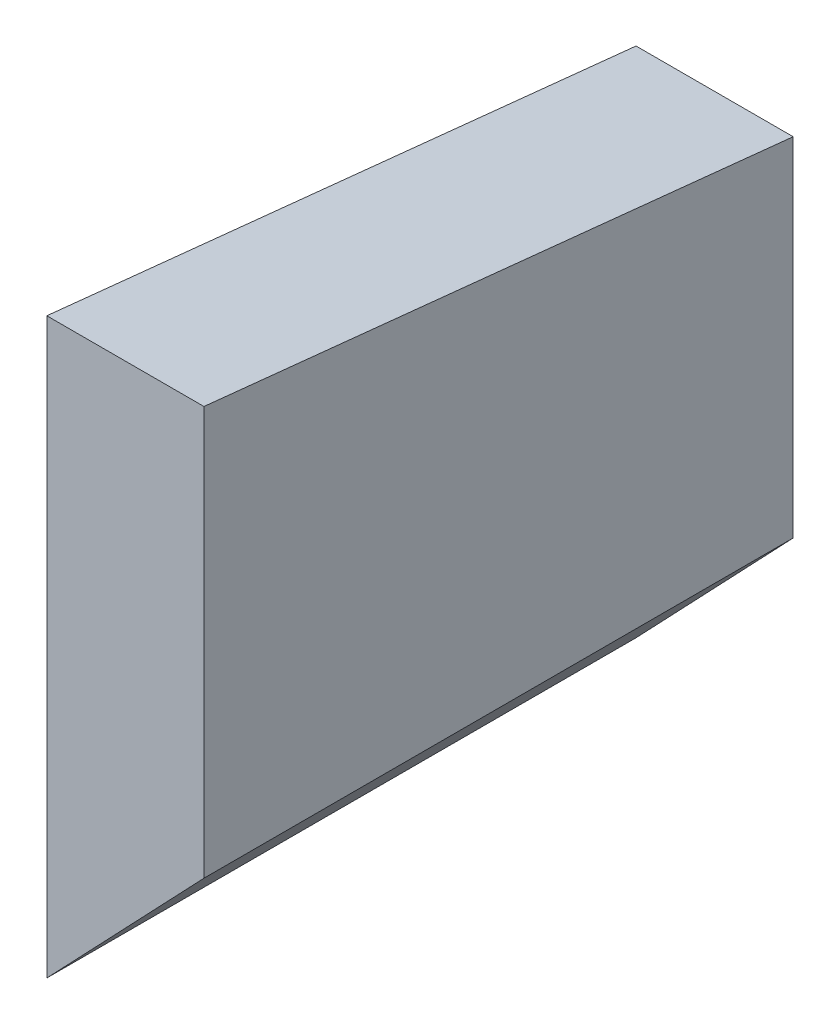
SolidWorks part; units mm, degrees
ref_plane "Plan de face" through (0, 0, 0) normal (0, 0, 1) x (1, 0, 0)
ref_plane "Plan de dessus" through (0, 0, 0) normal (0, 1, 0) x (1, 0, 0)
ref_plane "Plan de droite" through (0, 0, 0) normal (1, 0, 0) x (0, 0, -1)
sketch "Esquisse1" plane through (0, 0, 0) normal (0, 1, 0) x (1, 0, 0)
  line L1 (-2.54, 0) -> (2.54, 0)
  line L2 (-2.54, 0) -> (-2.54, -19.05)
  line L3 (-2.54, -19.05) -> (2.54, -19.05)
  line L4 (2.54, 0) -> (2.54, -19.05)
  point P4 (0, 0)
  dimension "D1" = 5.08
  dimension "D2" = 19.05
extrude "Boss.-Extru.1" add sketch "Esquisse1" against normal blind 20.828
sketch "Esquisse2" plane through (2.54, 0, 0) normal (1, 0, 0) x (0, 0, -1)
  line L3 (0, -1.972) -> (-19.05, 0)
  line L4 (0, -20.828) -> (0, 0) construction
  line L5 (-19.05, 0) -> (0, 0)
  line L6 (0, 0) -> (0, -1.972)
  line L7 (-19.05, 0) -> (0, 0) construction
  point P4 (0, 0)
  point P7 (0, 0)
  point P15 (0, 0)
  dimension "D1" = 84.09
extrude "Enlèv. mat.-Extru.1" cut sketch "Esquisse2" against normal through all
sketch "Esquisse3" plane through (0, 0, 19.05) normal (0, 0, 1) x (1, 0, 0)
  line L0 (-2.54, -20.828) -> (-2.54, -18.542)
  line L5 (-2.54, -18.542) -> (2.54, -13.208)
  line L6 (2.54, -20.828) -> (2.54, 0) construction
  line L7 (-2.54, -20.828) -> (-2.54, 0) construction
  line L11 (2.54, -13.208) -> (2.54, -20.828)
  line L12 (2.54, -20.828) -> (-2.54, -20.828)
  point P3 (0, 0)
  point P5 (0, 0)
  point P10 (0, 0)
  point P11 (-2.54, -20.6526)
  dimension "D1" = 7.62
  dimension "D2" = 2.286
extrude "Enlèv. mat.-Extru.2" cut sketch "Esquisse3" against normal through all
